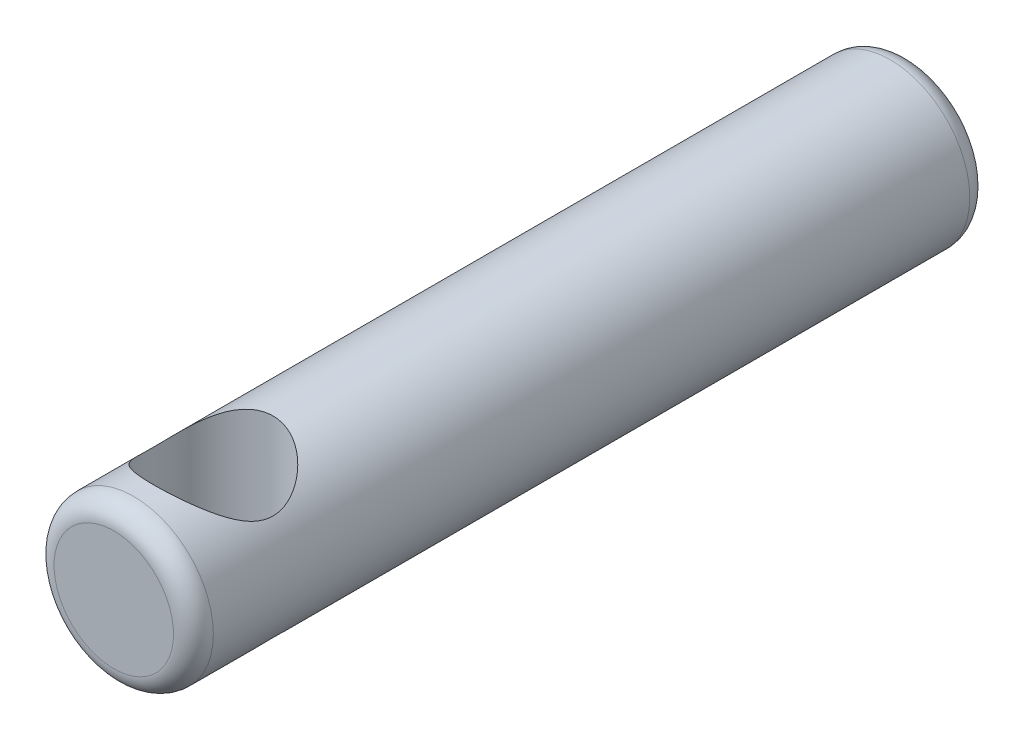
SolidWorks part; units mm, degrees
ref_plane "Front Plane" through (0, 0, 0) normal (0, 0, 1) x (1, 0, 0)
ref_plane "Top Plane" through (0, 0, 0) normal (0, 1, 0) x (1, 0, 0)
ref_plane "Right Plane" through (0, 0, 0) normal (1, 0, 0) x (0, 0, -1)
sketch "Sketch1" plane through (0, 0, 0) normal (0, 0, 1) x (1, 0, 0)
  circle A0 centre (0, 0) radius 2
  dimension "D1" = 4
extrude "Boss-Extrude1" add sketch "Sketch1" along normal blind 20
sketch "Sketch2" plane through (0, 0, 0) normal (0, 1, 0) x (1, 0, 0)
  line L0 (0, 0) -> (0, -17.5) construction
  circle A0 centre (0, -17.5) radius 1.5
  dimension "D2" = 3
  dimension "D1" = 17.5
extrude "Cut-Extrude1" cut sketch "Sketch2" against normal through all and the other way through all
fillet "Fillet1" radius 0.5 2 edges at (2, 0, 20) (2, 0, 0)
